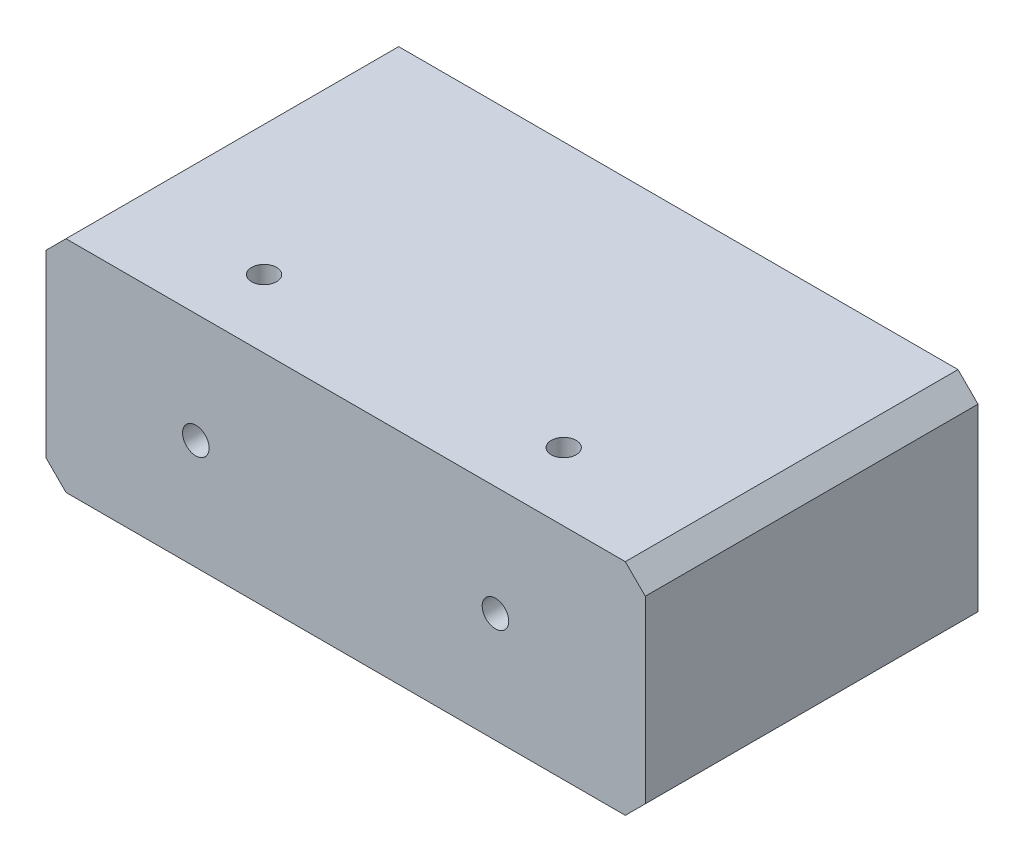
SolidWorks part; units mm, degrees
material "304, 316 OR 302 SSTL"
ref_plane "Front" through (0, 0, 0) normal (0, 0, 1) x (1, 0, 0)
ref_plane "Top" through (0, 0, 0) normal (0, 1, 0) x (1, 0, 0)
ref_plane "Right" through (0, 0, 0) normal (1, 0, 0) x (0, 0, -1)
sketch "Sketch1" plane through (0, 0, 0) normal (0, 1, 0) x (1, 0, 0)
  line L1 (76.2, -42.3037) -> (-76.2, -42.3037)
  line L2 (76.2, -42.3037) -> (76.2, 42.3037)
  line L3 (76.2, 42.3037) -> (-76.2, 42.3037)
  line L4 (-76.2, -42.3037) -> (-76.2, 42.3037)
  line L5 (76.2, -42.3037) -> (-76.2, 42.3037) construction
  line L6 (76.2, 42.3037) -> (-76.2, -42.3037) construction
  point P0 (0, 0)
  dimension "D1" = 152.4
  dimension "D2" = 84.6074
extrude "Extrude1" add sketch "Sketch1" along normal blind 55.88
hole_wizard "Tapped Hole for 1/4-20 Helicoil1" positions "Sketch3" profile "Sketch2" tap size "1/4-20" standard "Helicoil® Inch"
sketch "Sketch3" plane through (0, 0, 42.3037) normal (0, 0, 1) x (1, 0, 0)
  line L0 (-76.2, 55.88) -> (76.2, 55.88) construction
  line L1 (-76.2, 0) -> (76.2, 0) construction
  point P0 (-38.1, 27.94)
  point P1 (38.1, 27.94)
  point P8 (0, 0)
  dimension "D1" = 27.94
  dimension "D2" = 38.1
  dimension "D3" = 27.94
  dimension "D4" = 38.1
sketch "Sketch2" plane through (-38.1, 27.94, 42.3037) normal (1, 0, 0) x (0, -1, 0)
  line L0 (0, 0) -> (0, 21.7148)
  line L1 (0, 21.7148) -> (3.3782, 19.685)
  line L2 (3.3782, 19.685) -> (3.3782, 0)
  line L5 (3.3782, 0) -> (0, 0)
  line L10 (0, 21.7148) -> (-3.3782, 19.685) construction
  line L11 (0, -6.35) -> (0, 107.95) construction
  dimension "Tap Drill Dia." = 6.7564
  dimension "Tap Drill Depth" = 19.685
  dimension "Drill Angle" = 118
hole_wizard "1/4 (0.25) Diameter Hole1" positions "Sketch5" profile "Sketch4" hole size "1/4" standard "ANSI Inch"
sketch "Sketch5" plane through (0, 55.88, 0) normal (0, 1, 0) x (-1, 0, 0)
  point P0 (-38.161, 25.0114)
  point P4 (38.039, 25.0114)
  dimension "D1" = 76.2
sketch "Sketch4" plane through (38.161, 55.88, 25.0114) normal (1, 0, 0) x (0, 0, 1)
  line L0 (0, 0) -> (0, 29.8477)
  line L1 (0, 29.8477) -> (3.175, 27.94)
  line L2 (3.175, 27.94) -> (3.175, 0)
  line L5 (3.175, 0) -> (0, 0)
  line L10 (0, 29.8477) -> (-3.175, 27.94) construction
  line L11 (0, -6.35) -> (0, 107.95) construction
  dimension "Hole Dia." = 6.35
  dimension "Hole Depth" = 27.94
  dimension "Drill Angle" = 118
chamfer "Chamfer1" distance 5.08 angle 45 4 edges at (76.2, 55.88, 0) (76.2, 0, 0) (-76.2, 0, 0) (-76.2, 55.88, 0)
